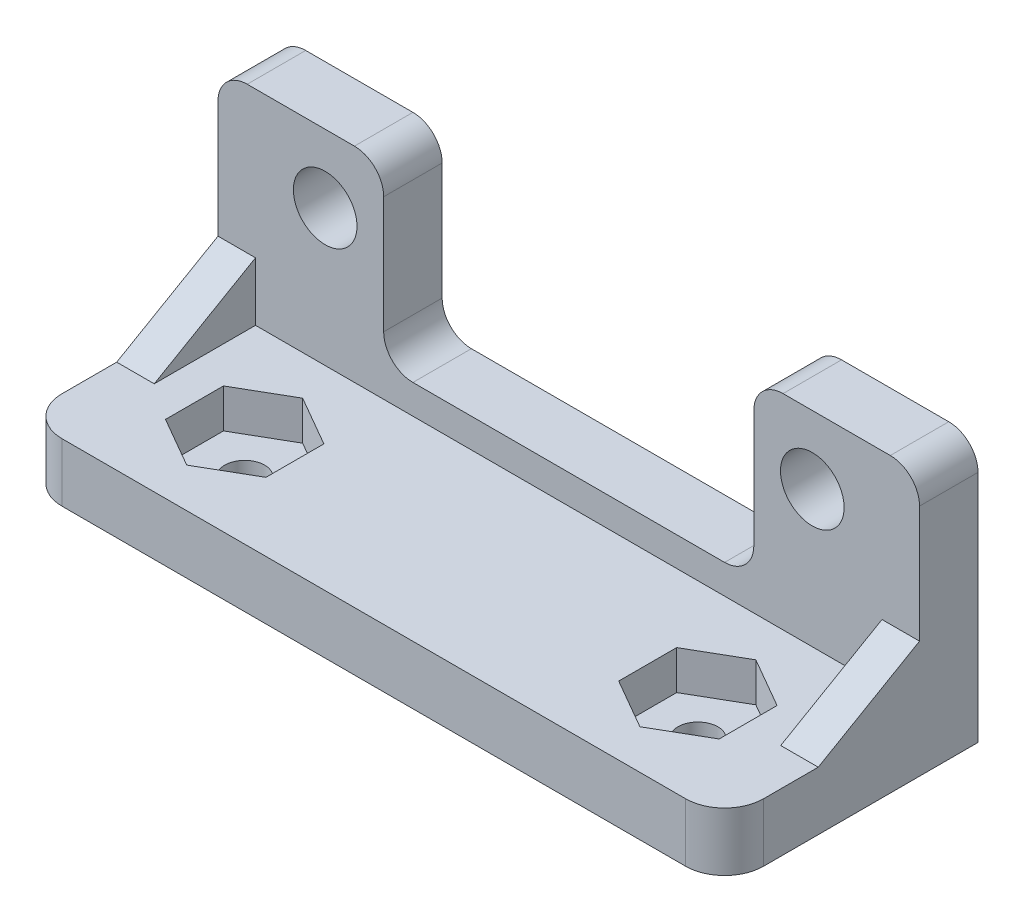
SolidWorks part; units mm, degrees
material "ABS"
ref_plane "Front Plane" through (0, 0, 0) normal (0, 0, 1) x (1, 0, 0)
ref_plane "Top Plane" through (0, 0, 0) normal (0, 1, 0) x (1, 0, 0)
ref_plane "Right Plane" through (0, 0, 0) normal (1, 0, 0) x (0, 0, -1)
sketch "Sketch1" plane through (0, 0, 0) normal (0, 0, 1) x (1, 0, 0)
  line L0 (-17.995, 0) -> (17.995, 0) construction
  line L3 (-17.995, 0) -> (-17.995, -10)
  line L4 (-17.995, -10) -> (17.995, -10)
  line L5 (17.995, 0) -> (17.995, -10)
  line L6 (-9.495, 0) -> (-9.495, -5.5)
  line L7 (-9.495, -5.5) -> (9.495, -5.5)
  line L8 (9.495, -5.5) -> (9.495, 0)
  line L9 (-17.995, 0) -> (-17.995, 3.5)
  line L10 (-17.995, 3.5) -> (-9.495, 3.5)
  line L11 (-9.495, 3.5) -> (-9.495, 0)
  line L12 (9.495, 0) -> (9.495, 3.5)
  line L13 (9.495, 3.5) -> (17.995, 3.5)
  line L14 (17.995, 3.5) -> (17.995, 0)
  point P0 (-12.495, 0)
  point P4 (0, 0)
  point P6 (12.495, 0)
  point P11 (0, 0)
  dimension "D2" = 3
  dimension "D3" = 3
  dimension "D1" = 8.5
  dimension "D4" = 5.5
  dimension "D5" = 10
  dimension "D6" = 8.5
  dimension "D7" = 24.99
  dimension "D8" = 3.5
extrude "Boss-Extrude1" add sketch "Sketch1" along normal blind 3
sketch "Sketch2" plane through (0, 0, 0) normal (0, 0, 1) x (1, 0, 0)
  line L0 (-17.995, 3.5) -> (-17.995, -10) construction
  line L1 (-17.995, -10) -> (17.995, -10)
  line L2 (-17.995, -10) -> (-17.995, -7)
  line L3 (-17.995, -7) -> (17.995, -7)
  line L4 (17.995, -10) -> (17.995, -7)
  point P6 (0, -7)
  dimension "D1" = 3
extrude "Boss-Extrude2" add sketch "Sketch2" along normal blind 13
sketch "Sketch3" plane through (0, -7, 0) normal (0, 1, 0) x (1, 0, 0)
  line L0 (-11.625, -8) -> (11.625, -8) construction
  line L1 (17.995, -13) -> (-17.995, -13) construction
  point P2 (0, -8)
  dimension "D1" = 23.25
  dimension "D2" = 5
hole_wizard "#4 Clearance Hole1" positions "Sketch4" profile "Sketch5" hole size "#4" standard "ANSI Inch" end condition through all
sketch "Sketch4" plane through (0, 0, 0) normal (0, 0, -1) x (-1, 0, 0)
  point P0 (12.495, 0)
  point P3 (-12.495, 0)
sketch "Sketch5" plane through (-12.495, 0, 0) normal (1, 0, 0) x (0, 1, 0)
  line L0 (0, 0) -> (0, 13)
  line L1 (0, 13) -> (1.6319, 13)
  line L2 (1.6319, 13) -> (1.6319, 0)
  line L5 (1.6319, 0) -> (0, 0)
  line L11 (0, -6.35) -> (0, 107.95) construction
  dimension "Thru Hole Dia." = 3.2639
  dimension "Thru Hole Depth" = 13
hole_wizard "M2.5x0.45 Tapped Hole1" positions "Sketch6" profile "Sketch7" tap size "M2.5x0.45" standard "ANSI Metric" end condition through all
sketch "Sketch6" plane through (0, -7, 0) normal (0, 1, 0) x (1, 0, 0)
  point P0 (-11.625, -8)
  point P3 (11.625, -8)
sketch "Sketch7" plane through (-11.625, -7, 8) normal (1, 0, 0) x (0, 0, 1)
  line L0 (0, 0) -> (0, 3)
  line L1 (0, 3) -> (1.025, 3)
  line L2 (1.025, 3) -> (1.025, 0)
  line L5 (1.025, 0) -> (0, 0)
  line L11 (0, -6.35) -> (0, 107.95) construction
  dimension "Thru Tap Drill Dia." = 2.05
  dimension "Thru Tap Drill Depth" = 3
sketch "Sketch9" plane through (0, -7, 0) normal (0, 1, 0) x (1, 0, 0)
  line L1 (-9.05, -6.5133) -> (-11.625, -5.0266)
  line L2 (-11.625, -5.0266) -> (-14.2, -6.5133)
  line L3 (-14.2, -6.5133) -> (-14.2, -9.4867)
  line L4 (-14.2, -9.4867) -> (-11.625, -10.9734)
  line L5 (-11.625, -10.9734) -> (-9.05, -9.4867)
  line L6 (-9.05, -9.4867) -> (-9.05, -6.5133)
  line L8 (11.625, -5.0266) -> (9.05, -6.5133)
  line L9 (9.05, -6.5133) -> (9.05, -9.4867)
  line L10 (9.05, -9.4867) -> (11.625, -10.9734)
  line L11 (11.625, -10.9734) -> (14.2, -9.4867)
  line L12 (14.2, -9.4867) -> (14.2, -6.5133)
  line L13 (14.2, -6.5133) -> (11.625, -5.0266)
  circle A0 centre (-11.625, -8) radius 2.575 construction
  circle A1 centre (11.625, -8) radius 2.575 construction
  dimension "D1" = 5.15
extrude "Cut-Extrude1" cut sketch "Sketch9" against normal blind 2 and the other way through all
fillet "Fillet1" radius 2 2 edges at (17.995, -8.5, 13) (-17.995, -8.5, 13)
sketch "Sketch8" plane through (-17.995, 0, 0) normal (-1, 0, 0) x (0, 0, 1)
  line L0 (3, -4) -> (8.1962, -7)
  line L2 (3, -7) -> (11, -7) construction
  line L3 (3, 3.5) -> (3, -7) construction
  dimension "D1" = 30
  dimension "D2" = 3
rib "Rib1" sketch "Sketch8" sketch "Sketch8" thickness 1.925 extrusion direction parallel to sketch draft on no parameters "D1"=1.925
mirror "Mirror1" about plane through (0, 0, 0) normal (1, 0, 0) of "Rib1"
fillet "Fillet2" radius 1.5 6 edges at (17.995, 3.5, 1.5) (9.495, 3.5, 1.5) (9.495, -5.5, 1.5) (-17.995, 3.5, 1.5) (-9.495, 3.5, 1.5) (-9.495, -5.5, 1.5)
